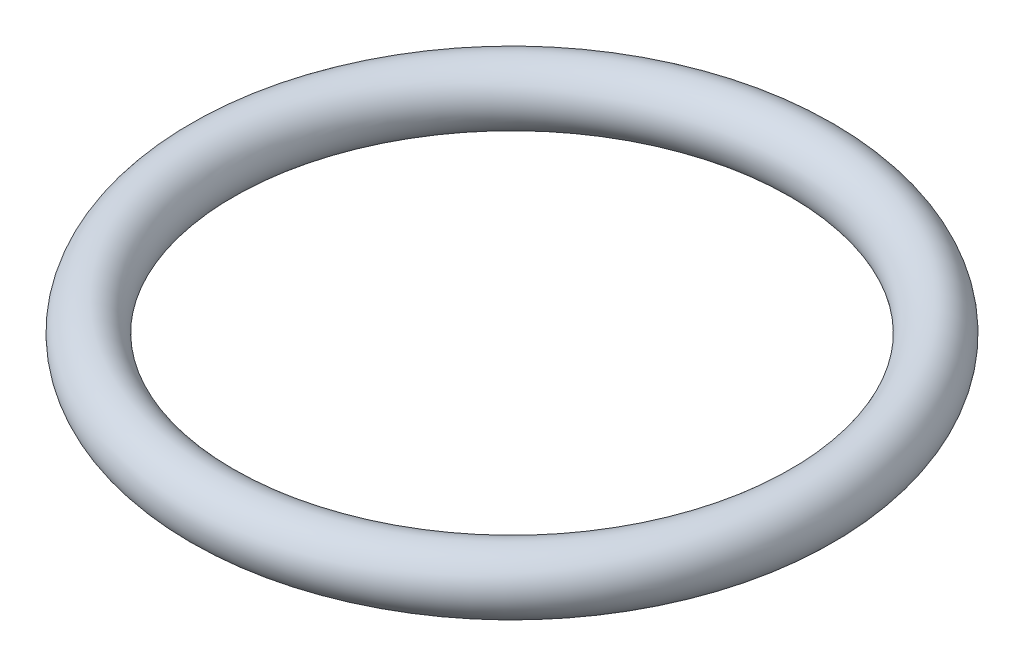
SolidWorks part; units mm, degrees
ref_plane "Face" through (0, 0, 0) normal (0, 0, 1) x (1, 0, 0)
ref_plane "Dessus" through (0, 0, 0) normal (0, 1, 0) x (1, 0, 0)
ref_plane "Droite" through (0, 0, 0) normal (1, 0, 0) x (0, 0, -1)
sketch "Esquisse1" plane through (0, 0, 0) normal (0, 0, 1) x (1, 0, 0)
  line L0 (0, 34.709) -> (0, -27.796) construction
  circle A0 centre (10, -2.7364) radius 1
  dimension "D1" = 2
  dimension "D2" = 10
revolve "Révolution1" add sketch "Esquisse1" angle 360 about L0
